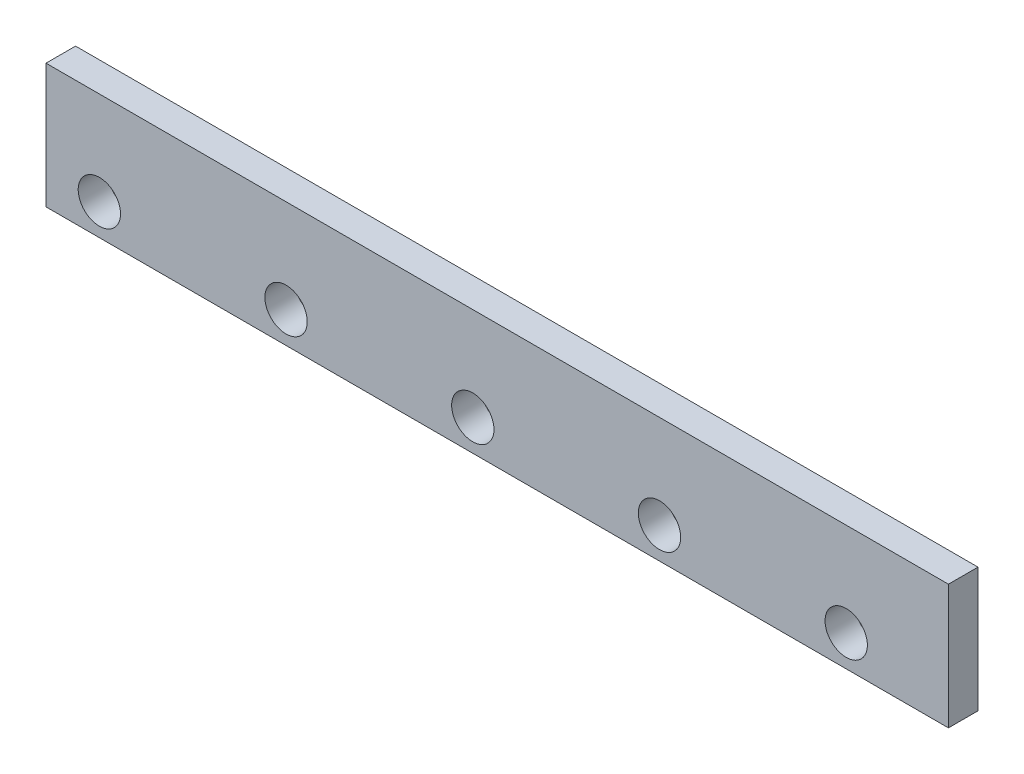
SolidWorks part; units mm, degrees
ref_plane "Front Plane" through (0, 0, 0) normal (0, 0, 1) x (1, 0, 0)
ref_plane "Top Plane" through (0, 0, 0) normal (0, 1, 0) x (1, 0, 0)
ref_plane "Right Plane" through (0, 0, 0) normal (1, 0, 0) x (0, 0, -1)
sketch "Sketch2" plane through (0, 0, 0) normal (0, 0, 1) x (1, 0, 0)
  line L0 (34.2992, 20.0015) -> (154.2992, 20.0015) construction
  line L1 (0, 0) -> (580, 0)
  line L2 (0, 0) -> (0, 80)
  line L3 (0, 80) -> (580, 80)
  line L4 (580, 0) -> (580, 80)
  circle A0 centre (34.2992, 20.0015) radius 13.6069
  circle A1 centre (154.2992, 20.0015) radius 13.6069
  circle A2 centre (274.2992, 20.0015) radius 13.6069
  circle A3 centre (394.2992, 20.0015) radius 13.6069
  circle A4 centre (514.2992, 20.0015) radius 13.6069
  dimension "D3" = 5
  dimension "D1" = 580
  dimension "D2" = 80
  dimension "D4" = 120
extrude "Boss-Extrude1" add sketch "Sketch2" along normal blind 19
